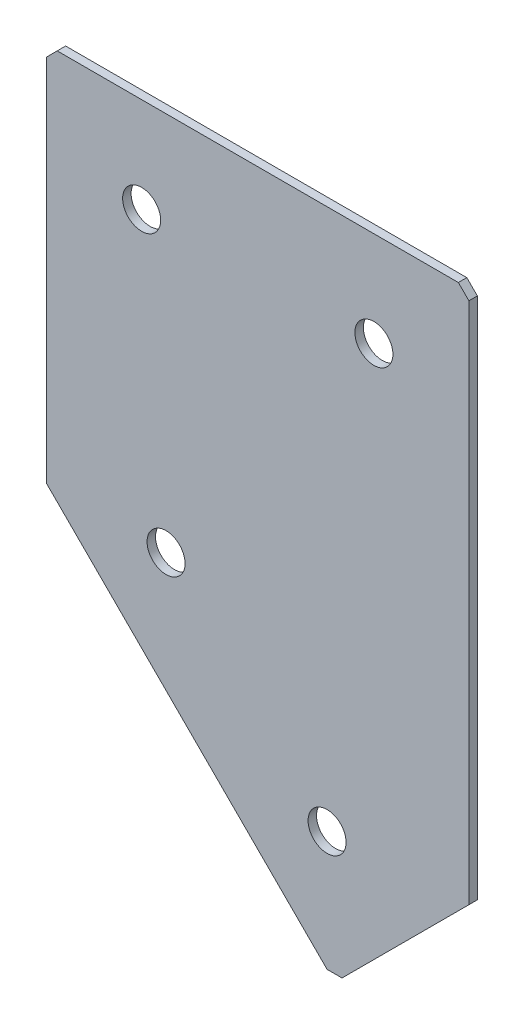
SolidWorks part; units mm, degrees
material "Простая углеродистая сталь"
ref_plane "Спереди" through (0, 0, 0) normal (0, 0, 1) x (1, 0, 0)
ref_plane "Сверху" through (0, 0, 0) normal (0, 1, 0) x (1, 0, 0)
ref_plane "Справа" through (0, 0, 0) normal (1, 0, 0) x (0, 0, -1)
sketch "Эскиз3" plane through (0, 0, 0) normal (0, 0, -1) x (1, 0, 0)
  line L0 (0, 0) -> (100, 0)
  line L1 (100, 0) -> (100, 126.3604)
  line L2 (0, 0) -> (0, 90)
  line L3 (0, 90) -> (68.1802, 158.1802)
  line L4 (68.1802, 158.1802) -> (100, 126.3604)
  dimension "D1" = 100
  dimension "D2" = 90
  dimension "D3" = 45
  dimension "D4" = 45
  dimension "D5" = 126.3604
extrude "Бобышка-Вытянуть1" add sketch "Эскиз3" along normal blind 2
hole_wizard "Отверстие с зазором M81" positions "Эскиз4" profile "Эскиз5" hole size "M8" standard "DIN" end condition through all
sketch "Эскиз4" plane through (0, 0, -2) normal (0, 0, -1) x (1, 0, 0)
  line L0 (28.2843, 90) -> (66.4124, 128.1282) construction
  line L2 (68.1802, 158.1802) -> (0, 90) construction
  line L3 (22.5, 22.5) -> (77.5, 22.5) construction
  line L5 (0, 0) -> (100, 0) construction
  line L6 (0, 90) -> (0, 0) construction
  line L7 (100, 0) -> (100, 126.3604) construction
  line L8 (100, 126.3604) -> (68.1802, 158.1802) construction
  line L9 (28.2843, 90) -> (0, 61.7157) construction
  point P0 (22.5, 22.5)
  point P2 (77.5, 22.5)
  point P4 (28.2843, 90)
  point P6 (66.4124, 128.1282)
  point P16 (22.5, 22.5)
  dimension "D1" = 22.5
  dimension "D2" = 20
  dimension "D3" = 22.5
  dimension "D4" = 22.5
  dimension "D5" = 22.5
  dimension "D6" = 40
  dimension "D7" = 53.9214
  dimension "D8" = 55
sketch "Эскиз5" plane through (22.5, -22.5, -2) normal (1, 0, 0) x (0, 1, 0)
  line L0 (0, 0) -> (0, 2)
  line L1 (0, 2) -> (4.5, 2)
  line L2 (4.5, 2) -> (4.5, 0)
  line L5 (4.5, 0) -> (0, 0)
  line L11 (0, -6.35) -> (0, 107.95) construction
  dimension "Диаметр сквозного отверстия" = 9
  dimension "Глубина сквозного отверстия" = 2
chamfer "Фаска1" distance 2.5 distance2 2.5 3 edges at (68.1802, -158.1802, -1) (100, 0, -1) (0, 0, -1)
